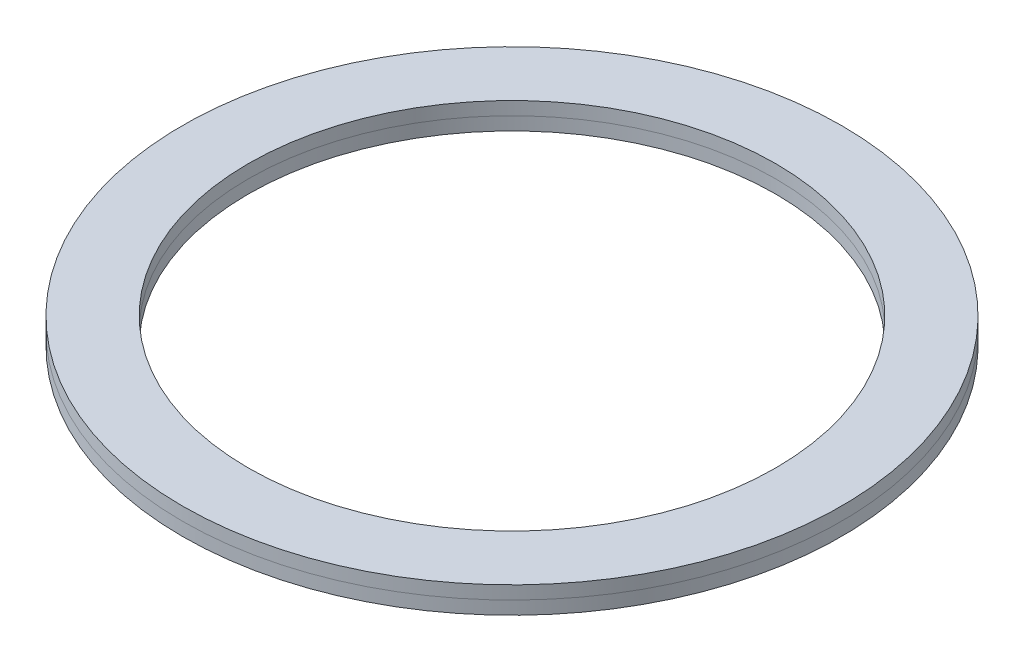
SolidWorks part; units mm, degrees
ref_plane "Front Plane" through (0, 0, 0) normal (0, 0, 1) x (1, 0, 0)
ref_plane "Top Plane" through (0, 0, 0) normal (0, 1, 0) x (1, 0, 0)
ref_plane "Right Plane" through (0, 0, 0) normal (1, 0, 0) x (0, 0, -1)
sketch "Sketch1" plane through (0, 0, 0) normal (0, 0, 1) x (1, 0, 0)
  line L0 (0, 0) -> (0, 35.3024) construction
  line L1 (-25, 0) -> (-20, 0)
  line L2 (-25, 0) -> (-25, 2)
  line L3 (-25, 2) -> (-20, 2)
  line L4 (-20, 0) -> (-20, 2)
  dimension "D1" = 40
  dimension "D2" = 50
  dimension "D3" = 2
revolve "Revolve1" add sketch "Sketch1" angle 360 about L0
ref_plane "Plane1" through (0, 1, 0) normal (0, 1, 0) x (1, 0, 0)
split "Split1" trim tools "Plane1" bodies to split 101 resulting bodies 105 106
